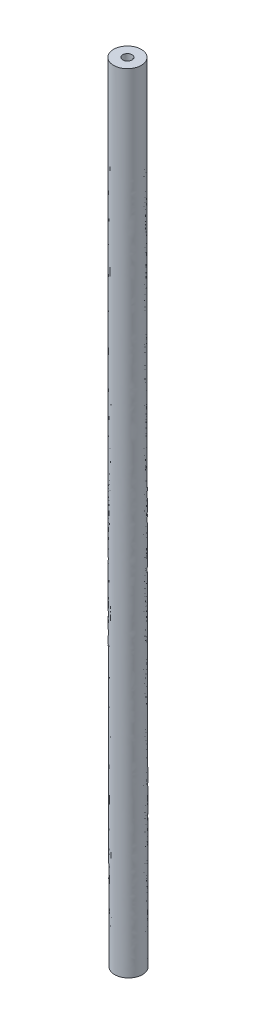
SolidWorks part; units mm, degrees
ref_plane "Front Plane" through (0, 0, 0) normal (0, 0, 1) x (1, 0, 0)
ref_plane "Top Plane" through (0, 0, 0) normal (0, 1, 0) x (1, 0, 0)
ref_plane "Right Plane" through (0, 0, 0) normal (1, 0, 0) x (0, 0, -1)
sketch "Sketch1" plane through (0, 0, 0) normal (0, 1, 0) x (1, 0, 0)
  circle A0 centre (0, 0) radius 1.5
  circle A1 centre (0, 0) radius 0.5
  dimension "D1" = 1
  dimension "D2" = 3
sketch "Sketch2" plane through (0, 0, 0) normal (0, 0, 1) x (1, 0, 0)
  line L0 (0.0625, -60) -> (0.125, -85)
  line L3 (0, -10) -> (0, 0)
  line L4 (0, -10) -> (0, -60) construction
  line L5 (0, -60) -> (0, -210) construction
  line L6 (0, -210) -> (0, -260) construction
  line L7 (0.125, -85) -> (0.4375, -210) construction
  arc A0 (0.0625, -60) -> (0, -10) centre (20000.0547, -10) cw
  arc A1 (0.4375, -210) -> (0.5, -260) centre (-19999.5547, -260) cw construction
  dimension "D1" = 50
  dimension "D2" = 150
  dimension "D3" = 10
  dimension "D4" = 25
  dimension "D5" = 0.5
sweep "Sweep1" add profiles "Sketch1" path "Sketch2"
